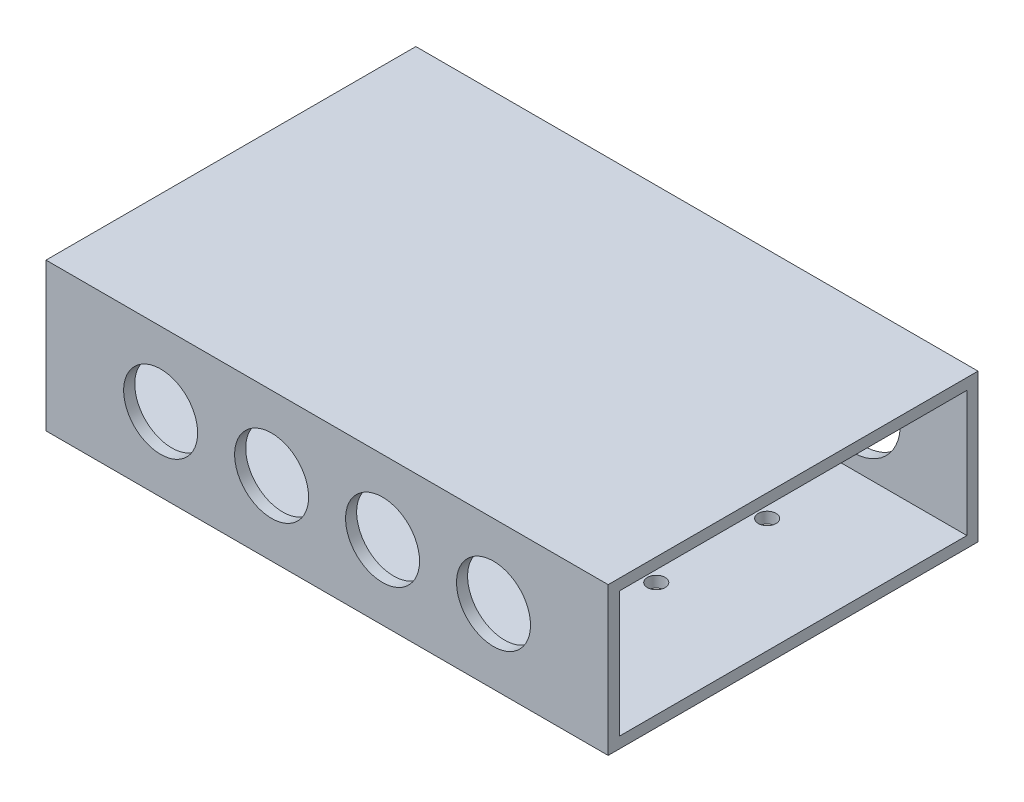
SolidWorks part; units mm, degrees
ref_plane "Front Plane" through (0, 0, 0) normal (0, 0, 1) x (1, 0, 0)
ref_plane "Top Plane" through (0, 0, 0) normal (0, 1, 0) x (1, 0, 0)
ref_plane "Right Plane" through (0, 0, 0) normal (1, 0, 0) x (0, 0, -1)
sketch "Sketch1" plane through (0, 0, 0) normal (0, 1, 0) x (1, 0, 0)
  line L1 (-26.4703, 33.7509) -> (49.5297, 33.7509)
  line L2 (-26.4703, 33.7509) -> (-26.4703, -16.2491)
  line L3 (-26.4703, -16.2491) -> (49.5297, -16.2491)
  line L4 (49.5297, 33.7509) -> (49.5297, -16.2491)
  dimension "D1" = 76
  dimension "D2" = 50
extrude "Boss-Extrude1" add sketch "Sketch1" along normal blind 20
sketch "Sketch2" plane through (-26.4703, 0, 0) normal (-1, 0, 0) x (0, 0, 1)
  line L0 (-33.7509, 0) -> (16.2491, 0) construction
  line L1 (14.7491, 1.5) -> (-32.2509, 1.5)
  line L2 (14.7491, 1.5) -> (14.7491, 18.5)
  line L3 (14.7491, 18.5) -> (-32.2509, 18.5)
  line L4 (-32.2509, 1.5) -> (-32.2509, 18.5)
  line L5 (-33.7509, 20) -> (16.2491, 20) construction
  line L6 (-33.7509, 20) -> (-33.7509, 0) construction
  line L7 (16.2491, 20) -> (16.2491, 0) construction
  dimension "D1" = 1.5
  dimension "D2" = 1.5
  dimension "D3" = 1.5
  dimension "D4" = 1.5
extrude "Cut-Extrude1" cut sketch "Sketch2" against normal blind 76
sketch "Sketch3" plane through (0, 0, -33.7509) normal (0, 0, -1) x (-1, 0, 0)
  line L0 (26.4703, 20) -> (26.4703, 0) construction
  line L1 (-49.5297, 20) -> (26.4703, 20) construction
  circle A0 centre (10.9703, 10) radius 6.5
  circle A1 centre (-4.0297, 10) radius 6.5
  circle A2 centre (-19.0297, 10) radius 6.5
  circle A3 centre (-34.0297, 10) radius 6.5
  point P2 (26.4703, 10)
  dimension "D1" = 15.5
  dimension "D2" = 10
  dimension "D3" = 4
extrude "Cut-Extrude2" cut sketch "Sketch3" against normal blind 2
sketch "Sketch4" plane through (0, 0, 16.2491) normal (0, 0, 1) x (1, 0, 0)
  line L0 (-26.4703, 20) -> (-26.4703, 0) construction
  line L1 (-26.4703, 0) -> (49.5297, 0) construction
  circle A0 centre (-10.9703, 10) radius 5
  circle A1 centre (4.0297, 10) radius 5
  circle A2 centre (19.0297, 10) radius 5
  circle A3 centre (34.0297, 10) radius 5
  point P2 (-26.4703, 10)
  dimension "D1" = 15.5
  dimension "D3" = 4
  dimension "D2" = 10
extrude "Cut-Extrude3" cut sketch "Sketch4" against normal blind 2
sketch "Sketch5" plane through (0, 0, 0) normal (0, -1, 0) x (-1, 0, 0)
  line L0 (-49.5297, 33.7509) -> (26.4703, 33.7509) construction
  line L2 (-49.5297, -16.2491) -> (-49.5297, 33.7509) construction
  circle A0 centre (-34.0297, 20.7509) radius 1.2
  circle A1 centre (-19.0297, 20.7509) radius 1.2
  circle A2 centre (-4.0297, 20.7509) radius 1.2
  circle A3 centre (10.9703, 20.7509) radius 1.2
  circle A4 centre (-19.0297, 5.7509) radius 1.2
  circle A5 centre (-4.0297, 5.7509) radius 1.2
  circle A6 centre (10.9703, 5.7509) radius 1.2
  circle A7 centre (-34.0297, 5.7509) radius 1.2
  dimension "D1" = 13
  dimension "D2" = 15.5
  dimension "D3" = 4
  dimension "D4" = 2
extrude "Cut-Extrude4" cut sketch "Sketch5" against normal blind 2
